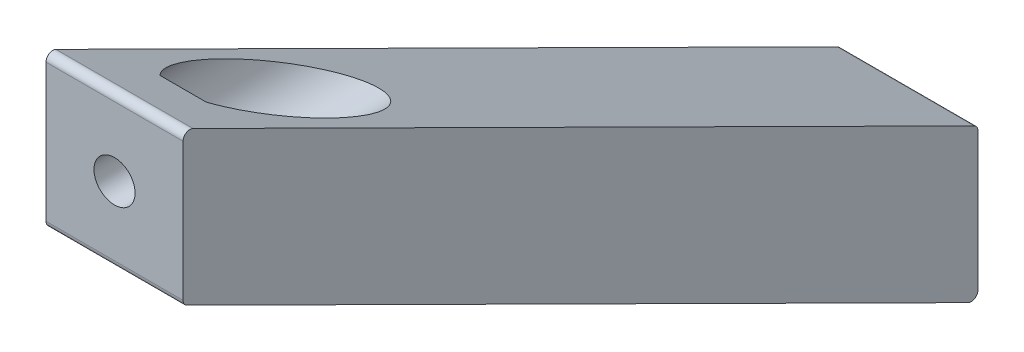
SolidWorks part; units mm, degrees
ref_plane "Front Plane" through (0, 0, 0) normal (0, 0, 1) x (1, 0, 0)
ref_plane "Top Plane" through (0, 0, 0) normal (0, 1, 0) x (1, 0, 0)
ref_plane "Right Plane" through (0, 0, 0) normal (1, 0, 0) x (0, 0, -1)
sketch "Sketch1" plane through (0, 0, 0) normal (1, 0, 0) x (0, 0, -1)
  line L1 (0.5549, 101.6843) -> (114.5549, 45.0135)
  line L3 (116, 45.9089) -> (116, 66.0103)
  line L4 (0, 122.6812) -> (0, 102.5798)
  line L5 (115.4451, 66.9058) -> (1.4451, 123.5767)
  arc A0 (114.5549, 45.0135) -> (116, 45.9089) centre (115, 45.9089) ccw
  arc A1 (116, 66.0103) -> (115.4451, 66.9058) centre (115, 66.0103) ccw
  arc A2 (0, 102.5798) -> (0.5549, 101.6843) centre (1, 102.5798) ccw
  arc A3 (1.4451, 123.5767) -> (0, 122.6812) centre (1, 122.6812) ccw
  point P6 (116, 44.2951)
  point P12 (0, 101.9601)
  point P15 (0, 124.2951)
  dimension "D4" = 1
  dimension "D1" = 116
  dimension "D2" = 80
  dimension "D3" = 20
extrude "Boss-Extrude1" add sketch "Sketch1" along normal blind 20
sketch "Sketch2" plane through (0, 0, 0) normal (0, 0, 1) x (1, 0, 0)
  line L4 (0, 112.6305) -> (12.2854, 112.6305) construction
  line L5 (0, 122.6812) -> (0, 102.5798) construction
  line L6 (20, 122.6812) -> (20, 102.5798) construction
  circle A2 centre (10, 112.6305) radius 3
  dimension "D1" = 10
  dimension "D3" = 6
extrude "Cut-Extrude5" cut sketch "Sketch2" against normal through all contours A2
sketch "Sketch5" plane through (0, 0, 0) normal (0, 0, 1) x (1, 0, 0)
  circle A0 centre (10, 112.6305) radius 7.5
  dimension "D1" = 15
extrude "Cut-Extrude6" cut sketch "Sketch5" against normal through all from offset 10 offset against normal yes
sketch "Sketch6" plane through (0, 0, -116) normal (0, 0, -1) x (-1, 0, 0)
  line L0 (-20, 55.9596) -> (0, 55.9596) construction
  line L1 (-20, 45.9089) -> (-20, 66.0103) construction
  line L2 (0, 45.9089) -> (0, 66.0103) construction
  circle A0 centre (-10, 55.9596) radius 3
  dimension "D1" = 6
extrude "Cut-Extrude7" cut sketch "Sketch6" against normal through all
sketch "Sketch7" plane through (0, 0, -116) normal (0, 0, -1) x (-1, 0, 0)
  circle A0 centre (-10, 55.9596) radius 7.5
  dimension "D1" = 15
extrude "Cut-Extrude8" cut sketch "Sketch7" against normal through all from offset 10
